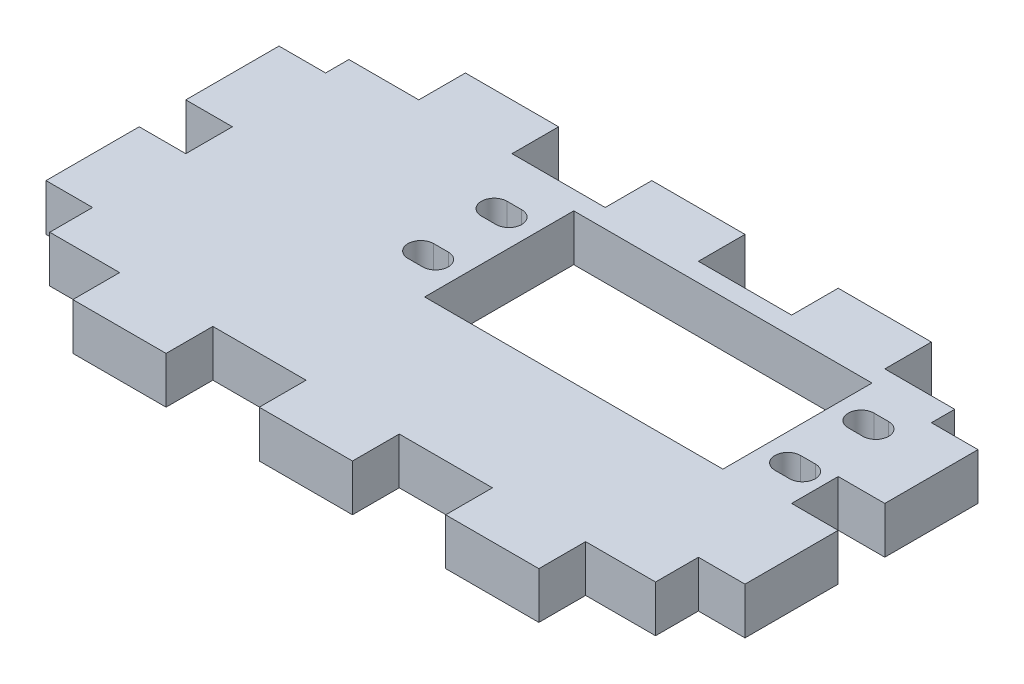
SolidWorks part; units mm, degrees
material "Pine"
ref_plane "Front Plane" through (0, 0, 0) normal (0, 0, 1) x (1, 0, 0)
ref_plane "Top Plane" through (0, 0, 0) normal (0, 1, 0) x (1, 0, 0)
ref_plane "Right Plane" through (0, 0, 0) normal (1, 0, 0) x (0, 0, -1)
sketch "Sketch1" plane through (0, 0, 0) normal (1, 0, 0) x (0, 0, -1)
  line L0 (0, 0) -> (21.4812, 245.5309)
  line L1 (145.7227, 304.8) -> (-70.1773, 304.8)
  line L2 (-70.1773, 304.8) -> (-70.1773, 298.45)
  line L3 (107.6227, 0) -> (107.6227, 304.8) construction
  line L4 (145.7227, 304.8) -> (145.7227, 0)
  line L5 (145.7227, 0) -> (0, 0)
  line L6 (44.1227, 285.75) -> (41.9532, 260.9527) construction
  line L7 (-19.3773, 304.8) -> (-19.3773, 269.1206) construction
  line L8 (-70.1773, 298.45) -> (21.4812, 245.5309)
  line L9 (6.3743, 0) -> (33.0408, 304.8) construction
  line L10 (6.9298, 6.35) -> (0.5556, 6.35) construction
  circle A0 centre (41.9532, 260.9527) radius 1.75
  point P12 (44.1227, 285.75)
  point P17 (6.9298, 6.35)
  point P20 (9.7076, 38.1)
  dimension "D6" = 3.5
  dimension "D1" = 304.8
  dimension "D2" = 85
  dimension "D3" = 38.1
  dimension "D4" = 50.8
  dimension "D5" = 30
  dimension "D7" = 101.6
  dimension "D8" = 19.05
  dimension "D9" = 24.892
  dimension "D10" = 19.05
  dimension "D11" = 5
  dimension "D12" = 6.35
  dimension "D13" = 127
  dimension "D14" = 6.35
  dimension "D15" = 6.35
  dimension "D16" = 38.1
sketch "Sketch2" plane through (0, 0, 0) normal (1, 0, 0) x (0, 0, -1)
  line L0 (145.7227, 304.8) -> (145.7227, 0) construction
  line L1 (3.3333, 31.75) -> (56.8227, 31.75)
  line L2 (3.3333, 31.75) -> (3.3333, 38.1)
  line L3 (3.3333, 38.1) -> (56.8227, 38.1)
  line L4 (56.8227, 31.75) -> (56.8227, 38.1)
  line L5 (0, 0) -> (21.4812, 245.5309) construction
  dimension "D1" = 88.9
  dimension "D2" = 6.35
  dimension "D3" = 31.75
extrude "Boss-Extrude1" add sketch "Sketch2" along normal blind 95.25
sketch "Sketch3" plane through (0, 38.1, 0) normal (0, 1, 0) x (1, 0, 0)
  line L0 (0, 145.7227) -> (0, 0) construction
  line L1 (0, 47.2977) -> (6.35, 47.2977)
  line L2 (0, 47.2977) -> (0, 53.6477)
  line L3 (0, 53.6477) -> (6.35, 53.6477)
  line L4 (6.35, 47.2977) -> (6.35, 53.6477)
  line L5 (95.25, 56.8227) -> (95.25, 3.3333) construction
  line L6 (95.25, 47.2977) -> (88.9, 47.2977)
  line L7 (95.25, 47.2977) -> (95.25, 53.6477)
  line L8 (95.25, 53.6477) -> (88.9, 53.6477)
  line L9 (88.9, 47.2977) -> (88.9, 53.6477)
  line L10 (95.25, 56.8227) -> (0, 56.8227) construction
  dimension "D1" = 9.525
  dimension "D2" = 6.35
  dimension "D3" = 6.35
extrude "Cut-Extrude1" cut sketch "Sketch3" against normal through all
pattern_linear "LPattern1" count 3 spacing 19.05 along (0, 0, 1) of "Cut-Extrude1"
sketch "Sketch5" plane through (0, 38.1, 0) normal (0, 1, 0) x (1, 0, 0)
  line L0 (95.25, 3.3333) -> (0, 3.3333) construction
  line L1 (0, 3.3333) -> (15.875, 3.3333)
  line L2 (0, 3.3333) -> (0, 9.7076)
  line L3 (0, 9.7076) -> (15.875, 9.7076)
  line L4 (15.875, 3.3333) -> (15.875, 9.7076)
  line L5 (28.575, 3.3333) -> (41.275, 3.3333)
  line L6 (28.575, 3.3333) -> (28.575, 9.7076)
  line L7 (28.575, 9.7076) -> (41.275, 9.7076)
  line L8 (41.275, 3.3333) -> (41.275, 9.7076)
  line L9 (95.25, 56.8227) -> (0, 56.8227) construction
  line L10 (53.975, 3.3333) -> (66.675, 3.3333)
  line L11 (53.975, 3.3333) -> (53.975, 9.7076)
  line L12 (53.975, 9.7076) -> (66.675, 9.7076)
  line L13 (66.675, 3.3333) -> (66.675, 9.7076)
  line L14 (95.25, 3.3333) -> (79.375, 3.3333)
  line L15 (95.25, 3.3333) -> (95.25, 9.7076)
  line L16 (95.25, 9.7076) -> (79.375, 9.7076)
  line L17 (79.375, 3.3333) -> (79.375, 9.7076)
  line L19 (0, 50.4727) -> (15.875, 50.4727)
  line L20 (0, 50.4727) -> (0, 56.8227)
  line L21 (0, 56.8227) -> (15.875, 56.8227)
  line L23 (95.25, 47.2977) -> (95.25, 34.5977) construction
  line L24 (28.575, 50.4727) -> (41.275, 50.4727)
  line L25 (28.575, 50.4727) -> (28.575, 56.8227)
  line L26 (28.575, 56.8227) -> (41.275, 56.8227)
  line L27 (41.275, 50.4727) -> (41.275, 56.8227)
  line L28 (53.975, 50.4727) -> (66.675, 50.4727)
  line L29 (53.975, 50.4727) -> (53.975, 56.8227)
  line L30 (53.975, 56.8227) -> (66.675, 56.8227)
  line L31 (66.675, 50.4727) -> (66.675, 56.8227)
  line L32 (79.375, 50.4727) -> (95.25, 50.4727)
  line L33 (79.375, 50.4727) -> (79.375, 56.8227)
  line L34 (79.375, 56.8227) -> (95.25, 56.8227)
  line L35 (95.25, 50.4727) -> (95.25, 56.8227)
  line L36 (15.875, 50.4727) -> (15.875, 56.8227)
  dimension "D1" = 12.7
  dimension "D2" = 12.7
  dimension "D3" = 12.7
  dimension "D4" = 12.7
  dimension "D5" = 6.35
extrude "Cut-Extrude2" cut sketch "Sketch5" against normal through all
sketch "Sketch7" plane through (0, 38.1, 0) normal (0, 1, 0) x (1, 0, 0)
  line L0 (83.85, 42.7727) -> (85.85, 42.7727) construction
  line L1 (80.17, 27.6127) -> (39.53, 27.6127)
  line L2 (80.17, 27.6127) -> (80.17, 47.9327)
  line L3 (80.17, 47.9327) -> (39.53, 47.9327)
  line L4 (39.53, 27.6127) -> (39.53, 47.9327)
  line L5 (80.17, 27.6127) -> (39.53, 47.9327) construction
  line L6 (80.17, 47.9327) -> (39.53, 27.6127) construction
  line L7 (83.85, 32.7727) -> (35.85, 32.7727) construction
  line L8 (83.85, 32.7727) -> (83.85, 42.7727) construction
  line L9 (83.85, 42.7727) -> (35.85, 42.7727) construction
  line L10 (35.85, 32.7727) -> (35.85, 42.7727) construction
  line L11 (83.85, 32.7727) -> (35.85, 42.7727) construction
  line L12 (83.85, 42.7727) -> (35.85, 32.7727) construction
  line L13 (83.85, 44.5227) -> (85.85, 44.5227)
  line L14 (83.85, 41.0227) -> (85.85, 41.0227)
  line L15 (83.85, 32.7727) -> (85.85, 32.7727) construction
  line L16 (83.85, 34.5227) -> (85.85, 34.5227)
  line L17 (83.85, 31.0227) -> (85.85, 31.0227)
  line L18 (35.85, 42.7727) -> (33.85, 42.7727) construction
  line L19 (35.85, 41.0227) -> (33.85, 41.0227)
  line L20 (35.85, 44.5227) -> (33.85, 44.5227)
  line L21 (35.85, 32.7727) -> (33.85, 32.7727) construction
  line L22 (35.85, 31.0227) -> (33.85, 31.0227)
  line L23 (35.85, 34.5227) -> (33.85, 34.5227)
  line L24 (59.85, 37.7727) -> (69.85, 37.7727) construction
  line L26 (28.575, 50.4727) -> (41.275, 50.4727) construction
  line L27 (88.9, 34.5977) -> (88.9, 28.2477) construction
  arc A0 (83.85, 44.5227) -> (83.85, 41.0227) centre (83.85, 42.7727) ccw
  arc A1 (85.85, 41.0227) -> (85.85, 44.5227) centre (85.85, 42.7727) ccw
  arc A2 (83.85, 34.5227) -> (83.85, 31.0227) centre (83.85, 32.7727) ccw
  arc A3 (85.85, 31.0227) -> (85.85, 34.5227) centre (85.85, 32.7727) ccw
  arc A4 (35.85, 41.0227) -> (35.85, 44.5227) centre (35.85, 42.7727) ccw
  arc A5 (33.85, 44.5227) -> (33.85, 41.0227) centre (33.85, 42.7727) ccw
  arc A6 (35.85, 31.0227) -> (35.85, 34.5227) centre (35.85, 32.7727) ccw
  arc A7 (33.85, 34.5227) -> (33.85, 31.0227) centre (33.85, 32.7727) ccw
  point P0 (59.85, 37.7727)
  point P5 (59.85, 37.7727)
  point P10 (84.85, 42.7727)
  point P16 (84.85, 32.7727)
  point P22 (34.85, 42.7727)
  point P28 (34.85, 32.7727)
  dimension "D6" = 1.75
  dimension "D1" = 10
  dimension "D2" = 48
  dimension "D3" = 20.32
  dimension "D4" = 40.64
  dimension "D5" = 2
  dimension "D7" = 14
  dimension "D8" = 19.05
  dimension "D9" = 12.7
extrude "Cut-Extrude4" cut sketch "Sketch7" against normal through all
